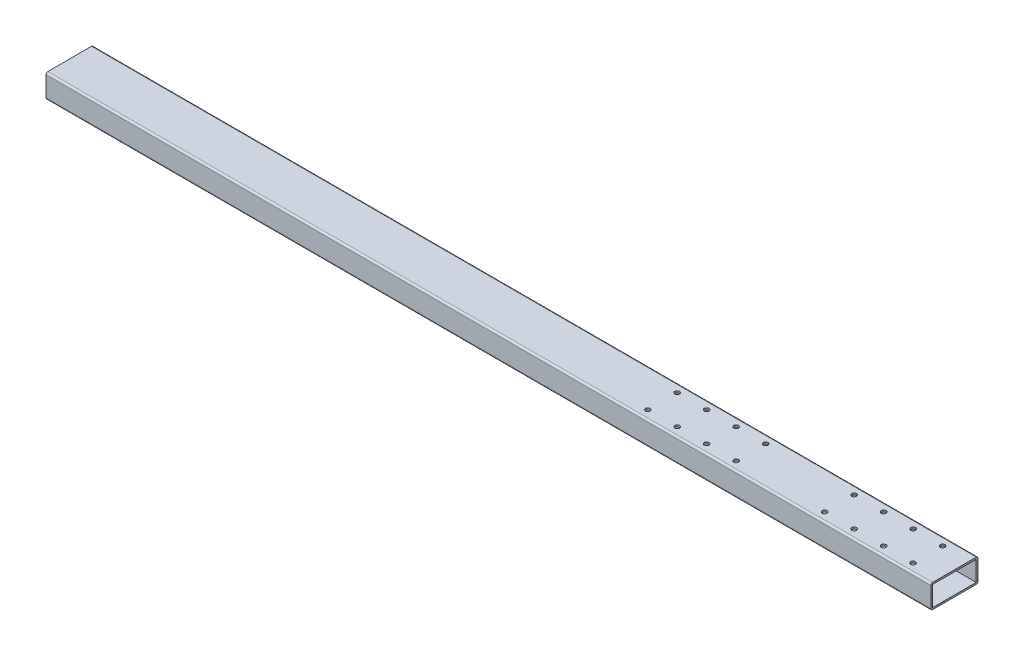
SolidWorks part; units mm, degrees
ref_plane "Спереди" through (0, 0, 0) normal (0, 0, 1) x (1, 0, 0)
ref_plane "Сверху" through (0, 0, 0) normal (0, 1, 0) x (1, 0, 0)
ref_plane "Справа" through (0, 0, 0) normal (1, 0, 0) x (0, 0, -1)
sketch "Эскиз1" plane through (0, 0, 0) normal (1, 0, 0) x (0, 0, -1)
  line L1 (-37, 20) -> (37, 20)
  line L2 (-40, 17) -> (-40, -17)
  line L3 (-37, -20) -> (37, -20)
  line L4 (40, 17) -> (40, -17)
  line L5 (-40, 20) -> (40, -20) construction
  line L6 (-40, -20) -> (40, 20) construction
  arc A0 (-37, 20) -> (-40, 17) centre (-37, 17) ccw
  arc A1 (-40, -17) -> (-37, -20) centre (-37, -17) ccw
  arc A2 (37, -20) -> (40, -17) centre (37, -17) ccw
  arc A3 (37, 20) -> (40, 17) centre (37, 17) cw
  point P0 (0, 0)
  dimension "D1" = 3
extrude "Вытянуть-Тонкостенный1" add sketch "Эскиз1" along normal blind 1500 thin
sketch "Эскиз2" plane through (0, 20, 0) normal (0, 1, 0) x (1, 0, 0)
  line L0 (778.6433, 0) -> (1509.4731, 0) construction
  circle A0 centre (1455, -25) radius 4.05
  circle A1 centre (1405, -25) radius 4.05
  circle A2 centre (1355, -25) radius 4.05
  circle A3 centre (1305, -25) radius 4.05
  circle A4 centre (1155, -25) radius 4.05
  circle A5 centre (1105, -25) radius 4.05
  circle A6 centre (1055, -25) radius 4.05
  circle A7 centre (1005, -25) radius 4.05
  circle A8 centre (1005, 25) radius 4.05
  circle A9 centre (1055, 25) radius 4.05
  circle A10 centre (1105, 25) radius 4.05
  circle A11 centre (1155, 25) radius 4.05
  circle A12 centre (1305, 25) radius 4.05
  circle A13 centre (1355, 25) radius 4.05
  circle A14 centre (1405, 25) radius 4.05
  circle A15 centre (1455, 25) radius 4.05
  dimension "D1" = 4
  dimension "D2" = 2
extrude "Вырез-Вытянуть1" cut sketch "Эскиз2" against normal through all
